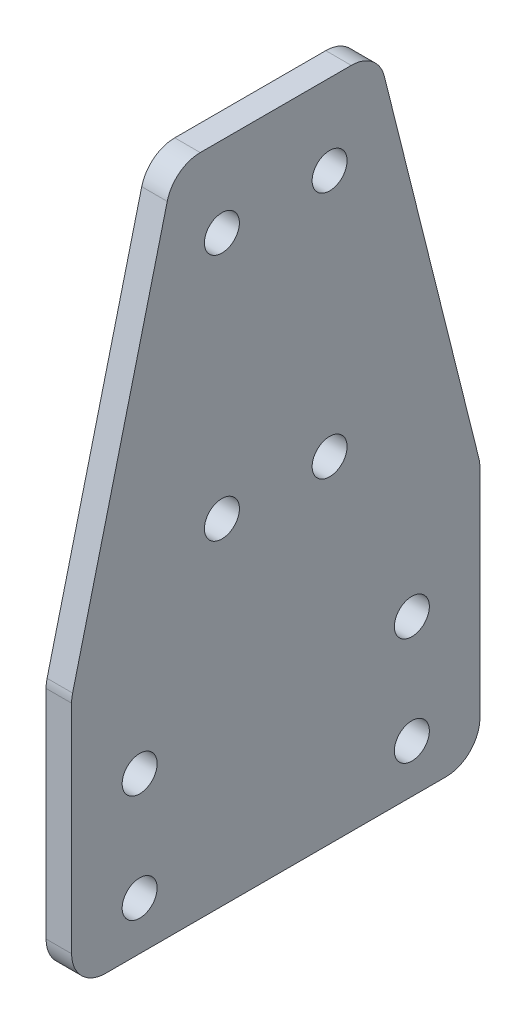
SolidWorks part; units mm, degrees
material "Alloy Steel"
ref_plane "Front Plane" through (0, 0, 0) normal (0, 0, 1) x (1, 0, 0)
ref_plane "Top Plane" through (0, 0, 0) normal (0, 1, 0) x (1, 0, 0)
ref_plane "Right Plane" through (0, 0, 0) normal (1, 0, 0) x (0, 0, -1)
ref_plane "Front Plane-Master Sketch" through (0, 0, 0) normal (0, 0, 1) x (1, 0, 0)
ref_plane "Top Plane-Master Sketch" through (0, 0, 0) normal (0, 1, 0) x (1, 0, 0)
ref_plane "Right Plane-Master Sketch" through (0, 0, 0) normal (1, 0, 0) x (0, 0, -1)
sketch "Y axis top-Master Sketch" plane through (0, 0, 0) normal (0, 1, 0) x (1, 0, 0)
  line L0 (140.4, -200) -> (120.4, -200)
  line L1 (-230.1875, -245) -> (230.1875, -245)
  line L2 (-230.1875, -245) -> (-230.1875, 245)
  line L3 (-230.1875, 245) -> (230.1875, 245)
  line L4 (230.1875, -245) -> (230.1875, 245)
  line L5 (0, 245) -> (0, -245) construction
  line L6 (-230.1875, 0) -> (230.1875, 0) construction
  line L7 (-8, 236.05) -> (8, 236.05)
  line L8 (-8, 236.05) -> (-8, -163.95)
  line L9 (-8, -163.95) -> (8, -163.95)
  line L10 (8, 236.05) -> (8, -163.95)
  line L11 (-140.4, 200) -> (-120.4, 200)
  line L12 (-140.4, 200) -> (-140.4, -200)
  line L13 (-140.4, -200) -> (-120.4, -200)
  line L14 (-120.4, 200) -> (-120.4, -200)
  line L15 (120.4, 200) -> (120.4, -200)
  line L16 (140.4, 200) -> (120.4, 200)
  line L17 (140.4, 200) -> (140.4, -200)
  line L18 (-230.1875, 206.9) -> (230.1875, 206.9)
  line L19 (-230.1875, -206.9) -> (230.1875, -206.9)
  line L20 (-192.0875, 206.9) -> (-192.0875, -206.9)
  line L21 (192.0875, 206.9) -> (192.0875, -206.9)
  line L22 (230.1875, 149.75) -> (192.0875, 149.75)
  line L27 (-152.4, -152.4) -> (152.4, -152.4)
  line L28 (-152.4, -152.4) -> (-152.4, 152.4)
  line L29 (-152.4, 152.4) -> (152.4, 152.4)
  line L34 (152.4, -152.4) -> (152.4, 152.4)
  line L35 (0, 152.4) -> (0, -152.4) construction
  line L36 (-152.4, 0) -> (152.4, 0) construction
  line L37 (-230.1875, 187.85) -> (-192.0875, 187.85)
  line L38 (-230.1875, 187.85) -> (-230.1875, 149.75)
  line L39 (-28.2, 324.7625) -> (28.2, 324.7625)
  line L40 (-28.2, 324.7625) -> (-28.2, 249.7625)
  line L41 (-28.2, 249.7625) -> (28.2, 249.7625)
  line L42 (28.2, 324.7625) -> (28.2, 249.7625)
  line L43 (-26, -20) -> (26, -20)
  line L44 (-26, -20) -> (-26, 20)
  line L45 (-26, 20) -> (26, 20)
  line L46 (26, -20) -> (26, 20)
  line L47 (0, 20) -> (0, -20) construction
  line L48 (-26, 0) -> (26, 0) construction
  line L49 (-230.1875, 149.75) -> (-192.0875, 149.75)
  line L50 (-192.0875, 187.85) -> (-192.0875, 149.75)
  line L51 (192.0875, 187.85) -> (192.0875, 149.75)
  line L52 (230.1875, 187.85) -> (192.0875, 187.85)
  line L53 (230.1875, 187.85) -> (230.1875, 149.75)
  line L55 (-230.1875, 206.9) -> (-234.95, 206.9)
  line L56 (-234.95, 206.9) -> (-234.95, 130.7)
  line L57 (-234.95, 130.7) -> (-230.1875, 130.7)
  point P0 (0, 0)
  point P8 (0, 236.05)
  point P32 (0, 0)
  point P33 (0, 324.7625)
  point P34 (0, 0)
  point P52 (-230.1875, 168.8)
  point P53 (-234.95, 168.8)
  point P56 (-120.4, 0)
  dimension "D3" = 16
  dimension "D4" = 400
  dimension "D5" = 20
  dimension "D6" = 400
  dimension "D7" = 38.1
  dimension "D8" = 38.1
  dimension "D9" = 38.1
  dimension "D10" = 12
  dimension "D11" = 56.4
  dimension "D12" = 75
  dimension "D13" = 4.7625
  dimension "D14" = 304.8
  dimension "D15" = 52
  dimension "D16" = 40
  dimension "D17" = 45
  dimension "D18" = 304.8
  dimension "D19" = 4.7625
  dimension "D20" = 19.05
  dimension "D22" = 8.95
  dimension "D23" = 460.375
ref_plane "X axis plane-Master Sketch" through (-230.1875, 0, -149.75) normal (0, 0, -1) x (-1, 0, 0)
sketch "Y axis side-Master Sketch" plane through (0, 0, 0) normal (0, 0, 1) x (1, 0, 0)
  line L0 (-230.1875, 0) -> (-230.1875, 47.625)
  line L3 (-230.1875, 0) -> (-192.0875, 0)
  line L4 (-23.5, 93.125) -> (-23.5, 46.125) construction
  line L6 (-230.1875, 38.1) -> (230.1875, 38.1)
  line L7 (230.1875, 0) -> (230.1875, 47.625)
  line L8 (-192.0875, 0) -> (-192.0875, 38.1)
  line L12 (230.1875, 0) -> (230.1875, 47.625)
  line L14 (230.1875, 0) -> (192.0875, 0)
  line L33 (192.0875, 0) -> (192.0875, 38.1)
  line L34 (-23.5, 46.125) -> (23.5, 46.125) construction
  line L41 (-230.1875, 47.625) -> (230.1875, 47.625)
  line L42 (-140.4, 47.625) -> (-140.4, 65.125)
  line L47 (-140.4, 65.125) -> (-120.4, 65.125)
  line L48 (-120.4, 65.125) -> (-120.4, 47.625)
  line L49 (140.4, 47.625) -> (140.4, 65.125)
  line L50 (140.4, 65.125) -> (120.4, 65.125)
  line L51 (120.4, 65.125) -> (120.4, 47.625)
  line L52 (-28.2, 41.425) -> (-28.2, 97.825)
  line L53 (-28.2, 97.825) -> (28.2, 97.825)
  line L54 (28.2, 97.825) -> (28.2, 41.425)
  line L55 (-152.4, 77.625) -> (-152.4, 52.225)
  line L56 (-152.4, 52.225) -> (-140.4, 52.225)
  line L57 (-152.4, 77.625) -> (-108.4, 77.625)
  line L58 (-108.4, 77.625) -> (-108.4, 52.225)
  line L59 (-108.4, 52.225) -> (-120.4, 52.225)
  line L60 (152.4, 52.225) -> (140.4, 52.225)
  line L61 (152.4, 77.625) -> (152.4, 52.225)
  line L62 (152.4, 77.625) -> (108.4, 77.625)
  line L63 (108.4, 77.625) -> (108.4, 52.225)
  line L64 (108.4, 52.225) -> (120.4, 52.225)
  line L65 (-28.2, 41.425) -> (28.2, 41.425)
  line L66 (-26, 49.625) -> (26, 49.625)
  line L67 (-26, 49.625) -> (-26, 89.625)
  line L68 (-26, 89.625) -> (26, 89.625)
  line L69 (26, 49.625) -> (26, 89.625)
  line L70 (0, 89.625) -> (0, 49.625) construction
  line L71 (-26, 69.625) -> (26, 69.625) construction
  line L73 (-152.4, 77.625) -> (-108.4, 77.625)
  line L74 (-152.4, 77.625) -> (-152.4, 89.625)
  line L75 (-152.4, 89.625) -> (-108.4, 89.625)
  line L76 (-108.4, 77.625) -> (-108.4, 89.625)
  line L77 (108.4, 77.625) -> (152.4, 77.625)
  line L78 (108.4, 77.625) -> (108.4, 89.625)
  line L79 (108.4, 89.625) -> (152.4, 89.625)
  line L80 (152.4, 77.625) -> (152.4, 89.625)
  line L85 (-152.4, 89.625) -> (152.4, 89.625)
  line L86 (-152.4, 89.625) -> (-152.4, 102.325)
  line L87 (-152.4, 102.325) -> (152.4, 102.325)
  line L88 (152.4, 89.625) -> (152.4, 102.325)
  circle A12 centre (0, 69.625) radius 6
  circle A13 centre (-23.5, 93.125) radius 2.5
  circle A14 centre (23.5, 93.125) radius 2.5
  circle A15 centre (23.5, 46.125) radius 2.5
  circle A16 centre (-23.5, 46.125) radius 2.5
  point P16 (0, 46.125)
  point P19 (-23.5, 69.625)
  point P90 (0, 97.825)
  point P91 (-28.2, 69.625)
  point P121 (0, 89.625)
  dimension "D20" = 12
  dimension "D24" = 22
  dimension "D5" = 5
  dimension "D3" = 38.1
  dimension "D4" = 47
  dimension "D16" = 9.525
  dimension "D18" = 17.5
  dimension "D19" = 56.4
  dimension "D21" = 44
  dimension "D22" = 30
  dimension "D23" = 4.6
  dimension "D25" = 40
  dimension "D26" = 52
  dimension "D28" = 12.7
sketch "X axis front-Master Sketch" plane through (-414.3375, 0, -149.75) normal (0, 0, -1) x (-1, 0, 0)
  line L0 (-184.15, 47.625) -> (-184.15, 390.525)
  line L1 (-184.15, 390.525) -> (-222.25, 390.525)
  line L2 (-222.25, 390.525) -> (-222.25, 47.625)
  line L4 (-414.3375, 0) -> (-414.3375, 246.425) construction
  line L5 (-644.525, 47.625) -> (-644.525, 390.525)
  line L6 (-644.525, 390.525) -> (-606.425, 390.525)
  line L7 (-606.425, 390.525) -> (-606.425, 47.625)
  line L8 (-222.25, 390.525) -> (-606.425, 390.525)
  line L9 (-222.25, 352.425) -> (-606.425, 352.425)
  line L10 (-222.25, 284.525) -> (-606.425, 284.525)
  line L11 (-222.25, 246.425) -> (-606.425, 246.425)
  line L12 (-414.3375, 390.525) -> (-414.3375, 352.425) construction
  line L13 (-414.3375, 284.525) -> (-414.3375, 246.425) construction
  line L14 (-414.3375, 352.425) -> (-414.3375, 284.525) construction
  line L15 (-614.3375, 381.475) -> (-214.3375, 381.475)
  line L16 (-614.3375, 381.475) -> (-614.3375, 361.475)
  line L17 (-614.3375, 361.475) -> (-214.3375, 361.475)
  line L18 (-214.3375, 381.475) -> (-214.3375, 361.475)
  line L19 (-614.3375, 275.475) -> (-214.3375, 275.475)
  line L20 (-614.3375, 275.475) -> (-614.3375, 255.475)
  line L21 (-614.3375, 255.475) -> (-214.3375, 255.475)
  line L22 (-214.3375, 275.475) -> (-214.3375, 255.475)
  line L23 (-614.3375, 326.475) -> (-214.3375, 326.475)
  line L24 (-614.3375, 326.475) -> (-614.3375, 310.475)
  line L25 (-614.3375, 310.475) -> (-214.3375, 310.475)
  line L26 (-214.3375, 326.475) -> (-214.3375, 310.475)
  line L27 (-184.15, 47.625) -> (-222.25, 47.625)
  line L28 (-606.425, 47.625) -> (-644.525, 47.625)
  line L29 (-434.3375, 344.475) -> (-394.3375, 344.475)
  line L30 (-434.3375, 344.475) -> (-434.3375, 292.475)
  line L31 (-434.3375, 292.475) -> (-394.3375, 292.475)
  line L32 (-394.3375, 344.475) -> (-394.3375, 292.475)
  point P24 (-414.3375, 344.475)
  point P25 (-614.3375, 265.475)
  point P30 (-614.3375, 371.475)
  point P31 (-414.3375, 371.475)
  point P36 (-414.3375, 265.475)
  point P41 (-414.3375, 326.475)
  point P42 (-414.3375, 318.475)
  point P43 (-614.3375, 318.475)
  point P44 (-394.3375, 318.475)
  point P45 (-214.3375, 318.475)
  point P51 (-414.3375, 381.475)
  dimension "D1" = 38.1
  dimension "D2" = 400
  dimension "D3" = 20
  dimension "D4" = 16
  dimension "D5" = 40
  dimension "D6" = 52
  dimension "D7" = 35
  dimension "D8" = 342.9
sketch "X axis side-Master Sketch" plane through (0, 0, 0) normal (1, 0, 0) x (0, 0, -1)
  line L1 (144.9875, 381.475) -> (127.4875, 381.475)
  line L2 (144.9875, 381.475) -> (144.9875, 361.475)
  line L3 (144.9875, 361.475) -> (127.4875, 361.475)
  line L4 (127.4875, 381.475) -> (127.4875, 361.475)
  line L5 (140.3875, 381.475) -> (140.3875, 393.475)
  line L6 (140.3875, 393.475) -> (114.9875, 393.475)
  line L7 (114.9875, 393.475) -> (114.9875, 349.475)
  line L8 (144.9875, 371.475) -> (127.4875, 371.475) construction
  line L10 (140.3875, 349.475) -> (114.9875, 349.475)
  line L11 (140.3875, 361.475) -> (140.3875, 349.475)
  line L12 (149.75, 390.525) -> (144.9875, 390.525)
  line L14 (144.9875, 390.525) -> (144.9875, 352.425)
  line L15 (144.9875, 352.425) -> (149.75, 352.425)
  line L17 (149.75, 318.475) -> (122.9875, 318.475) construction
  line L18 (144.9875, 284.525) -> (149.75, 284.525)
  line L19 (144.9875, 246.425) -> (144.9875, 284.525)
  line L20 (149.75, 246.425) -> (144.9875, 246.425)
  line L21 (140.3875, 275.475) -> (140.3875, 287.475)
  line L22 (140.3875, 287.475) -> (114.9875, 287.475)
  line L23 (114.9875, 243.475) -> (114.9875, 287.475)
  line L24 (140.3875, 243.475) -> (114.9875, 243.475)
  line L25 (140.3875, 255.475) -> (140.3875, 243.475)
  line L26 (127.4875, 255.475) -> (127.4875, 275.475)
  line L27 (144.9875, 275.475) -> (127.4875, 275.475)
  line L28 (144.9875, 255.475) -> (144.9875, 275.475)
  line L29 (144.9875, 255.475) -> (127.4875, 255.475)
  line L31 (102.9875, 344.475) -> (142.9875, 344.475)
  line L32 (102.9875, 344.475) -> (102.9875, 292.475)
  line L33 (102.9875, 292.475) -> (142.9875, 292.475)
  line L34 (142.9875, 344.475) -> (142.9875, 292.475)
  line L35 (102.9875, 493.475) -> (96.6375, 493.475)
  line L36 (102.9875, 493.475) -> (102.9875, 243.475)
  line L37 (102.9875, 243.475) -> (96.6375, 243.475)
  line L38 (96.6375, 493.475) -> (96.6375, 243.475)
  circle A0 centre (122.9875, 318.475) radius 6
  point P14 (114.9875, 265.475)
  point P16 (114.9875, 371.475)
  point P48 (122.9875, 292.475)
  dimension "D7" = 12
  dimension "D9" = 22
  dimension "D1" = 4.7625
  dimension "D2" = 17.5
  dimension "D3" = 12
  dimension "D4" = 12.5
  dimension "D5" = 25.4
  dimension "D6" = 40
  dimension "D8" = 6.35
  dimension "D10" = 250
ref_plane "Z axis front plane-Master Sketch" through (0, 493.475, -96.6375) normal (0, 0, 1) x (1, 0, 0)
sketch "Z axis front-Master Sketch" plane through (0, 493.475, -96.6375) normal (0, 0, 1) x (1, 0, 0)
  line L0 (0, 48.55) -> (0, -276.85) construction
  line L1 (-103, 48.55) -> (103, 48.55)
  line L2 (-103, 48.55) -> (-103, -276.85)
  line L3 (-103, -276.85) -> (103, -276.85)
  line L4 (103, 48.55) -> (103, -276.85)
  line L5 (-88, 35.85) -> (-68, 35.85)
  line L6 (-88, 35.85) -> (-88, -264.15)
  line L7 (-88, -264.15) -> (-68, -264.15)
  line L8 (-68, 35.85) -> (-68, -264.15)
  line L9 (88, -264.15) -> (68, -264.15)
  line L10 (68, 35.85) -> (68, -264.15)
  line L11 (88, 35.85) -> (68, 35.85)
  line L12 (88, 35.85) -> (88, -264.15)
  line L13 (-103, -114.15) -> (103, -114.15) construction
  line L14 (-8, -20.3536) -> (8, -20.3536)
  line L15 (-8, -20.3536) -> (-8, -229.2947)
  line L16 (-8, -229.2947) -> (8, -229.2947)
  line L17 (8, -20.3536) -> (8, -229.2947)
  line L19 (-26, -43.6221) -> (26, -43.6221)
  line L20 (-26, -43.6221) -> (-26, -83.6221)
  line L21 (-26, -83.6221) -> (26, -83.6221)
  line L22 (26, -43.6221) -> (26, -83.6221)
  point P20 (0, -20.3536)
  point P27 (0, -43.6221)
  dimension "D1" = 15
  dimension "D2" = 20
  dimension "D3" = 300
  dimension "D4" = 16
  dimension "D5" = 40
  dimension "D6" = 52
  dimension "D7" = 42
  dimension "D8" = 12.7
  dimension "D10" = 12.7
ref_plane "Z axis side plane-Master Sketch" through (-103, 379.325, -96.6375) normal (0, -1, 0) x (-1, 0, 0)
inserted part "Master Sketch"
move or copy body "Body-Move/Copy2"
ref_plane "Plane1" through (-230.1875, 0, 0) normal (1, 0, 0) x (0, 0, -1)
sketch "Sketch1" plane through (-230.1875, 0, 0) normal (1, 0, 0) x (0, 0, -1)
  line L0 (130.7, 0) -> (206.9, 0)
  line L1 (-245, 0) -> (245, 0) construction
  line L2 (-245, 0) -> (245, 0) construction
  line L3 (187.85, 0) -> (149.75, 0) construction
  line L4 (206.9, 0) -> (206.9, 47.625)
  line L6 (130.7, 47.625) -> (130.7, 0)
  line L7 (206.9, 47.625) -> (187.85, 123.825)
  line L8 (187.85, 123.825) -> (149.75, 123.825)
  line L9 (149.75, 123.825) -> (130.7, 47.625)
  line L11 (143.4, 38.1) -> (-238.65, 38.1) construction
  line L13 (158.75, 108.825) -> (158.75, 123.825) construction
  line L15 (149.75, 390.525) -> (149.75, 38.1) construction
  line L16 (168.8, 123.825) -> (168.8, 0) construction
  line L17 (178.85, 108.825) -> (158.75, 108.825) construction
  line L18 (238.65, 47.625) -> (194.2, 47.625) construction
  circle A0 centre (194.2, 29.1) radius 3.2639
  circle A2 centre (158.75, 108.825) radius 3.2639
  circle A5 centre (178.85, 108.825) radius 3.2639
  circle A6 centre (178.85, 85.725) radius 3.2639 construction
  circle A7 centre (178.85, 62.625) radius 3.2639
  circle A8 centre (158.75, 85.725) radius 3.2639 construction
  circle A9 centre (158.75, 62.625) radius 3.2639
  circle A10 centre (168.8, 29.1) radius 3.2639 construction
  circle A11 centre (143.4, 29.1) radius 3.2639
  circle A12 centre (168.8, 9) radius 3.2639 construction
  circle A13 centre (143.4, 9) radius 3.2639
  circle A14 centre (194.2, 9) radius 3.2639
  point P8 (168.8, 0)
  point P9 (168.8, 123.825)
  point P44 (168.8, 108.825)
  dimension "D3" = 6.5278
  dimension "D2" = 76.2
  dimension "D7" = 12.7
  dimension "D1" = 15
  dimension "D4" = 9
  dimension "D8" = 15
  dimension "D9" = 9
  dimension "D10" = 9
  dimension "D12" = 2
  dimension "D5" = 3
  dimension "D11" = 3
  dimension "D6" = 2
extrude "Boss-Extrude1" add sketch "Sketch1" against normal up to vertex
sketch "Sketch3" plane through (-234.95, 0, 0) normal (-1, 0, 0) x (0, 0, 1)
  line L0 (-187.85, 123.825) -> (-187.85, 198.825)
  line L1 (-187.85, 198.825) -> (-149.75, 198.825)
  line L2 (-149.75, 198.825) -> (-30.7, 38.1)
  line L3 (-30.7, 38.1) -> (-30.7, 0)
  line L4 (-30.7, 0) -> (-130.7, 0)
  line L5 (-130.7, 47.625) -> (-130.7, 0) construction
  line L6 (-149.75, 123.825) -> (-130.7, 47.625) construction
  line L7 (-187.85, 123.825) -> (-149.75, 123.825) construction
  line L8 (-130.7, 47.625) -> (-130.7, 0)
  line L9 (-149.75, 123.825) -> (-130.7, 47.625)
  line L10 (-187.85, 123.825) -> (-149.75, 123.825)
  line L11 (-178.85, 108.825) -> (-178.85, 62.625) construction
  line L12 (-158.75, 108.825) -> (-158.75, 62.625) construction
  line L13 (-178.85, 198.825) -> (-178.85, 189.825) construction
  line L14 (-178.85, 189.825) -> (-187.85, 189.825) construction
  line L15 (-178.85, 108.825) -> (-178.85, 149.325) construction
  line L16 (-178.85, 149.325) -> (-178.85, 189.825) construction
  line L17 (-194.2, 9) -> (-143.4, 9) construction
  line L18 (-143.4, 29.1) -> (-194.2, 29.1) construction
  line L19 (-143.4, 29.1) -> (-91.55, 29.1) construction
  line L20 (-91.55, 29.1) -> (-39.7, 29.1) construction
  line L21 (-39.7, 9) -> (-30.7, 9) construction
  line L22 (-39.7, 9) -> (-39.7, 0) construction
  circle A0 centre (-158.75, 108.825) radius 3.2639 construction
  circle A1 centre (-178.85, 62.625) radius 3.2639 construction
  circle A2 centre (-178.85, 149.325) radius 3.2639
  circle A3 centre (-178.85, 189.825) radius 3.2639
  circle A4 centre (-158.75, 189.825) radius 3.2639
  circle A5 centre (-158.75, 149.325) radius 3.2639
  circle A6 centre (-91.55, 29.1) radius 3.2639
  circle A7 centre (-39.7, 29.1) radius 3.2639
  circle A8 centre (-39.7, 9) radius 3.2639
  circle A9 centre (-91.55, 9) radius 3.2639
  circle A10 centre (-143.4, 29.1) radius 3.2639 construction
  dimension "D1" = 100
  dimension "D2" = 75
extrude "Boss-Extrude2" [suppressed] add sketch "Sketch3" against normal up to surface (4.7625 mm away)
fillet "Fillet1" radius 6.35 6 edges at (-232.5687, 0, -130.7) (-232.5687, 0, -206.9) (-232.5687, 47.625, -206.9) (-232.5687, 47.625, -130.7) (-232.5687, 123.825, -187.85) (-232.5687, 123.825, -149.75)
fillet "Fillet2" [suppressed] radius 10
equation "\"D3@Sketch1\"=.257in"
